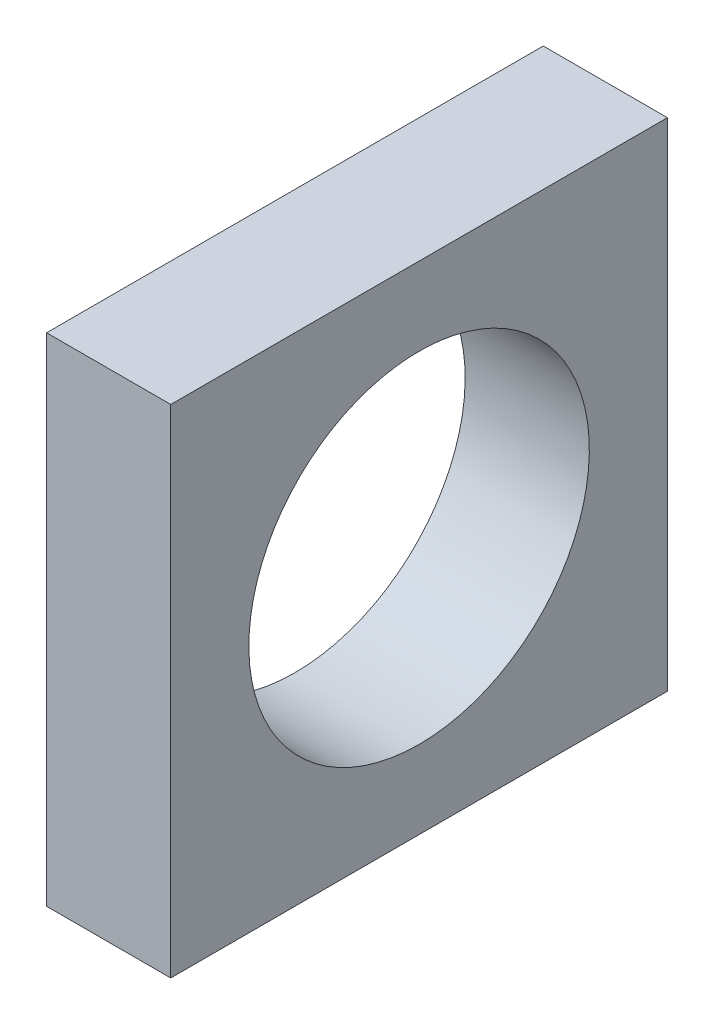
SolidWorks part; units mm, degrees
ref_plane "Front Plane" through (0, 0, 0) normal (0, 0, 1) x (1, 0, 0)
ref_plane "Top Plane" through (0, 0, 0) normal (0, 1, 0) x (1, 0, 0)
ref_plane "Right Plane" through (0, 0, 0) normal (1, 0, 0) x (0, 0, -1)
sketch "Sketch1" plane through (0, 0, 0) normal (0, 0, 1) x (1, 0, 0)
  line L1 (5.1477, -28.7494) -> (11.4977, -28.7494)
  line L2 (5.1477, -28.7494) -> (5.1477, -3.3494)
  line L3 (5.1477, -3.3494) -> (11.4977, -3.3494)
  line L4 (11.4977, -28.7494) -> (11.4977, -3.3494)
  dimension "D1" = 6.35
  dimension "D2" = 25.4
extrude "Boss-Extrude1" add sketch "Sketch1" along normal blind 25.4
sketch "Sketch3" plane through (5.1477, 0, 0) normal (-1, 0, 0) x (0, 0, 1)
  circle A0 centre (12.7, -16.0494) radius 8.7312 construction
  circle A1 centre (12.7, -16.0494) radius 8.7313
  circle A2 centre (12.7, -16.0494) radius 8.7058
  dimension "D1" = 0.0254
sketch "Sketch4" plane through (5.1477, 0, 0) normal (-1, 0, 0) x (0, 0, 1)
  circle A0 centre (12.7, -16.0494) radius 6.4416 construction
  circle A1 centre (12.7, -16.0494) radius 6.4416
extrude "Cut-Extrude1" cut sketch "Sketch4" against normal up to surface (6.35 mm away) up to face at (11.4977, -16.0494, 12.7)
extrude "Cut-Extrude2" cut sketch "Sketch3" against normal up to surface (6.35 mm away) contours A2
